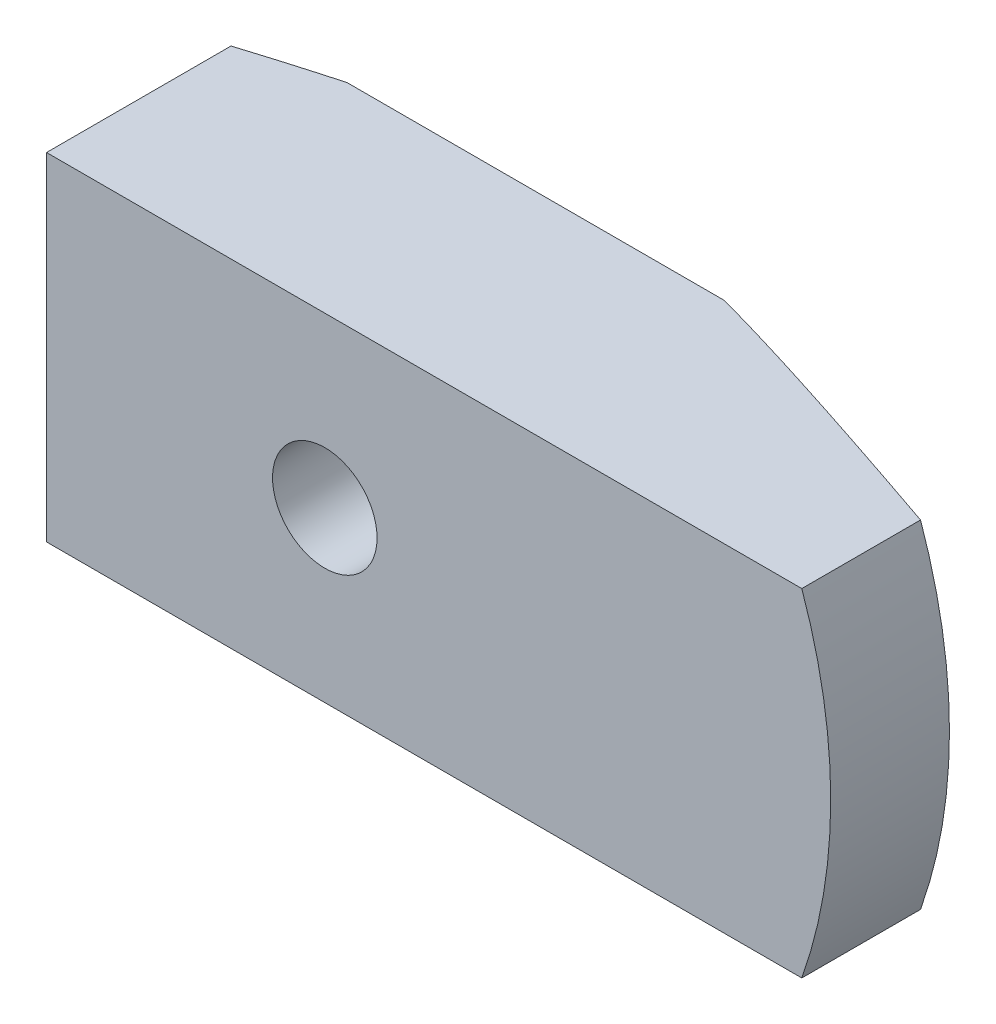
SolidWorks part; units mm, degrees
ref_plane "Front Plane" through (0, 0, 0) normal (0, 0, 1) x (1, 0, 0)
ref_plane "Top Plane" through (0, 0, 0) normal (0, 1, 0) x (1, 0, 0)
ref_plane "Right Plane" through (0, 0, 0) normal (1, 0, 0) x (0, 0, -1)
sketch "Sketch1" plane through (0, 0, 0) normal (0, 0, 1) x (1, 0, 0)
  circle A0 centre (0, 0) radius 38.1
  dimension "D1" = 76.2
extrude "Boss-Extrude1" add sketch "Sketch1" along normal blind 15.875
sketch "Sketch2" plane through (0, 0, 15.875) normal (0, 0, 1) x (1, 0, 0)
  circle A0 centre (0, 0) radius 3.937
  dimension "D1" = 7.874
extrude "Cut-Extrude1" cut sketch "Sketch2" against normal blind 5.715
sketch "Sketch3" plane through (0, 0, 10.16) normal (0, 0, 1) x (1, 0, 0)
  circle A0 centre (0, 0) radius 2.4506
extrude "Cut-Extrude2" cut sketch "Sketch3" against normal through all
chamfer "Chamfer1" distance 19.05 angle 20 1 edges at (38.1, 0, 0)
sketch "Sketch4" plane through (0, 0, 15.875) normal (0, 0, 1) x (1, 0, 0)
  line L0 (-20.955, 12.7) -> (-20.955, -12.7)
  line L1 (51.1179, -12.7) -> (-51.1179, -12.7)
  line L2 (51.1179, -12.7) -> (51.1179, 12.7)
  line L3 (51.1179, 12.7) -> (-51.1179, 12.7)
  line L4 (-51.1179, -12.7) -> (-51.1179, 12.7)
  line L5 (51.1179, -12.7) -> (-51.1179, 12.7) construction
  line L6 (51.1179, 12.7) -> (-51.1179, -12.7) construction
  point P0 (0, 0)
  circle M8 centre (0, 0) radius 38.1
  dimension "D1" = 25.4
  dimension "D2" = 20.955
extrude "Cut-Extrude3" cut sketch "Sketch4" against normal through all contours L0 L3 L1 M8 | L3 M8 | L1 M8
